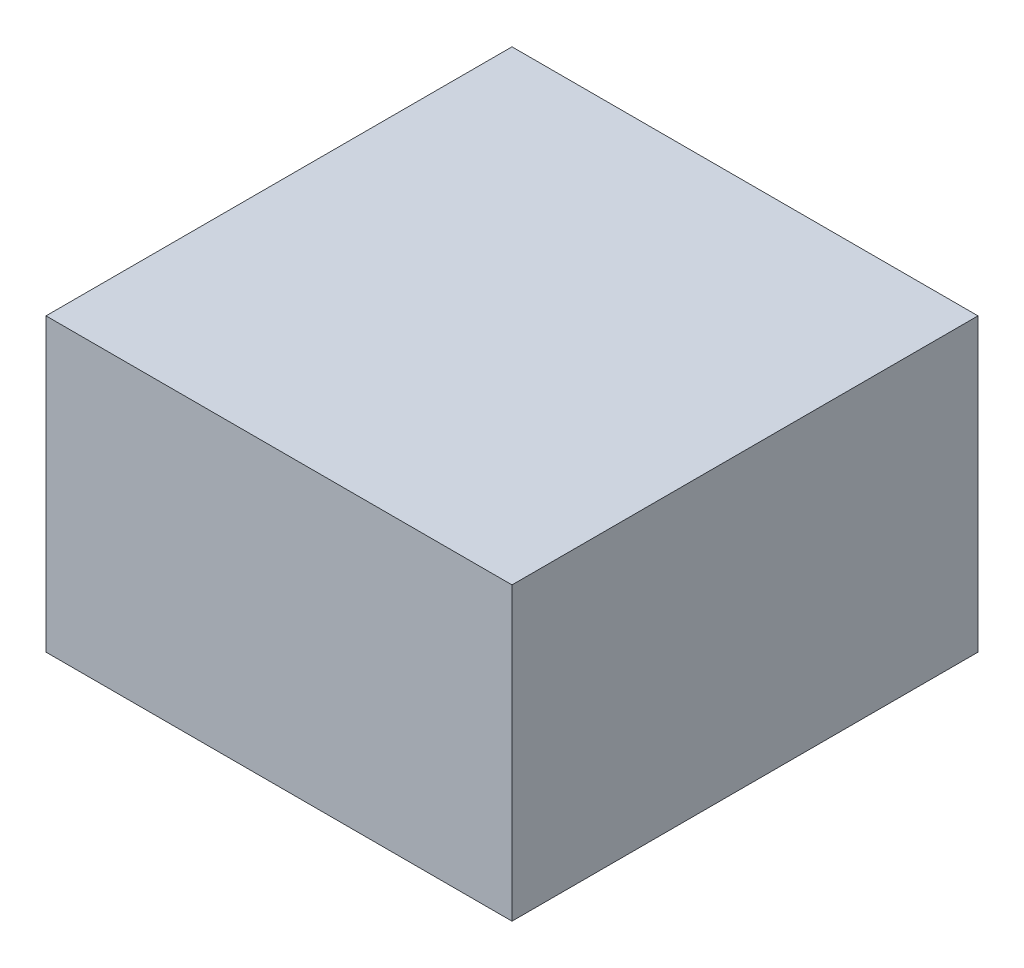
SolidWorks part; units mm, degrees
ref_plane "Front Plane" through (0, 0, 0) normal (0, 0, 1) x (1, 0, 0)
ref_plane "Top Plane" through (0, 0, 0) normal (0, 1, 0) x (1, 0, 0)
ref_plane "Right Plane" through (0, 0, 0) normal (1, 0, 0) x (0, 0, -1)
sketch "Sketch1" plane through (0, 0, 0) normal (0, 1, 0) x (1, 0, 0)
  line L1 (101.6, -101.6) -> (-101.6, -101.6)
  line L2 (101.6, -101.6) -> (101.6, 101.6)
  line L3 (101.6, 101.6) -> (-101.6, 101.6)
  line L4 (-101.6, -101.6) -> (-101.6, 101.6)
  line L5 (0, 101.6) -> (0, -101.6) construction
  line L6 (101.6, 0) -> (-101.6, 0) construction
  point P0 (0, 0)
  dimension "D1" = 203.2
  dimension "D2" = 203.2
extrude "Boss-Extrude1" add sketch "Sketch1" along normal blind 127
